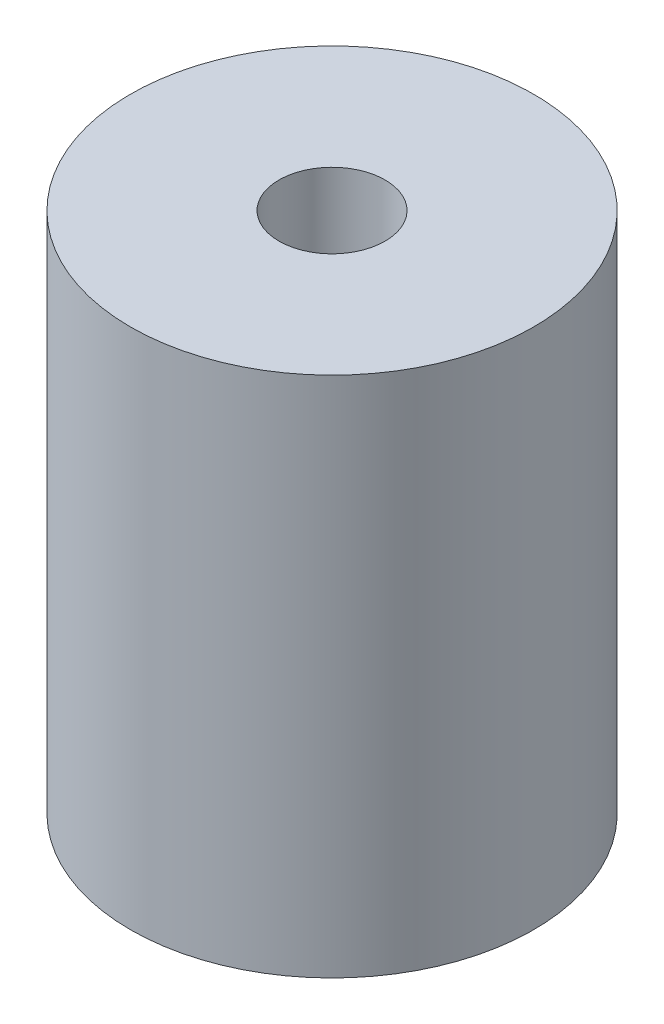
SolidWorks part; units mm, degrees
ref_plane "Front" through (0, 0, 0) normal (0, 0, 1) x (1, 0, 0)
ref_plane "Top" through (0, 0, 0) normal (0, 1, 0) x (1, 0, 0)
ref_plane "Right" through (0, 0, 0) normal (1, 0, 0) x (0, 0, -1)
sketch "Sketch1" plane through (0, 0, 0) normal (0, 1, 0) x (1, 0, 0)
  circle A0 centre (0, 0) radius 9.5
  dimension "D1" = 19
extrude "coupling body" add sketch "Sketch1" along normal blind 24.6 contours A0
sketch "Sketch2" plane through (0, 24.6, 0) normal (0, 1, 0) x (1, 0, 0)
  circle A0 centre (0, 0) radius 2.5
  dimension "D1" = 5
extrude "5mm hole" cut sketch "Sketch2" against normal up to next
sketch "Sketch3" plane through (0, 0, 0) normal (0, -1, 0) x (1, 0, 0)
  circle A0 centre (0, 0) radius 4
  dimension "D1" = 8
extrude "8 mm hole" cut sketch "Sketch3" against normal blind 17.25
